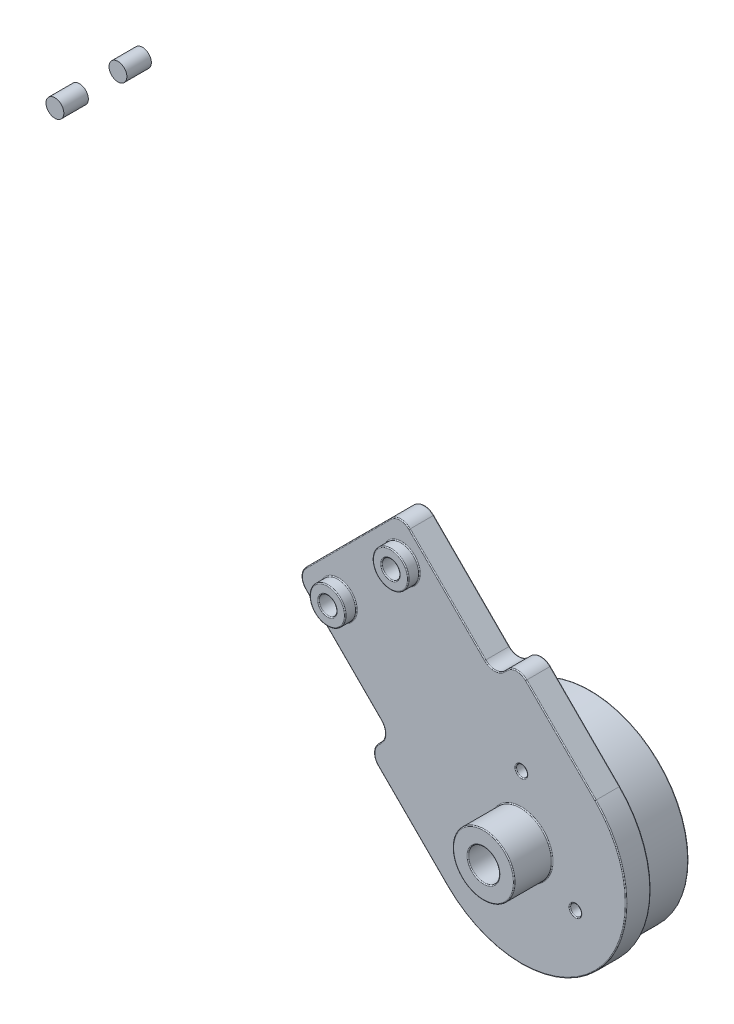
SolidWorks part; units mm, degrees
ref_plane "Front Plane" through (0, 0, 0) normal (0, 0, 1) x (1, 0, 0)
ref_plane "Top Plane" through (0, 0, 0) normal (0, 1, 0) x (1, 0, 0)
ref_plane "Right Plane" through (0, 0, 0) normal (1, 0, 0) x (0, 0, -1)
sketch "Sketch1" plane through (0, 0, 0) normal (0, 0, 1) x (1, 0, 0)
  line L0 (-100, 0) -> (100, 0) construction
  line L1 (-100, 0) -> (0, 100) construction
  line L2 (0, 100) -> (100, 0) construction
  line L3 (0, 0) -> (-50, 50) construction
  line L4 (-40, 60) -> (40, 60) construction
  line L5 (0, 100) -> (0, 60) construction
  line L6 (-56.5165, 43.4835) -> (-40, 60)
  line L7 (-40, 60) -> (40, 60)
  line L8 (40, 60) -> (86.565, 13.435) construction
  line L9 (-49.4454, 36.4124) -> (-35.8579, 50)
  line L10 (-35.8579, 50) -> (35.8579, 50)
  line L11 (35.8579, 50) -> (79.4939, 6.364)
  line L12 (-63.5876, 50.5546) -> (-44.1421, 70)
  line L13 (-44.1421, 70) -> (44.1421, 70)
  line L14 (44.1421, 70) -> (93.636, 20.5061)
  line L15 (-63.5876, 50.5546) -> (-49.4454, 36.4124)
  line L16 (93.636, 20.5061) -> (79.4939, 6.364)
  line L17 (91.1612, 18.0312) -> (104.5962, 4.5962)
  line L18 (81.9688, 8.8388) -> (95.4038, -4.5962)
  line L19 (58.2807, 55.8614) -> (44.1386, 41.7193) construction
  line L20 (6, 70) -> (3.4304, 82.6944)
  line L21 (-6, 70) -> (-3.4304, 82.6944)
  line L22 (40, 60) -> (86.565, 13.435)
  circle A0 centre (-100, 0) radius 20
  circle A1 centre (0, 0) radius 20
  circle A2 centre (100, 0) radius 20
  circle A3 centre (100, 0) radius 10 construction
  circle A4 centre (100, 0) radius 3.5
  arc A5 (95.4038, -4.5962) -> (104.5962, 4.5962) centre (100, 0) ccw
  circle A6 centre (100, 0) radius 6.5 construction
  circle A7 centre (47.6741, 45.2548) radius 1
  circle A8 centre (54.7452, 52.3259) radius 1
  circle A9 centre (0, 60) radius 1.5
  circle A10 centre (0, 82) radius 1.5
  arc A11 (3.4304, 82.6944) -> (-3.4304, 82.6944) centre (0, 82) ccw
  circle A12 centre (0, 82) radius 3.5 construction
  circle A13 centre (-50, 50) radius 1.5
  point P2 (0, 0)
  dimension "D5" = 40
  dimension "D9" = 20
  dimension "D10" = 7
  dimension "D14" = 2
  dimension "D17" = 3
  dimension "D22" = 3
  dimension "D1" = 200
  dimension "D2" = 90
  dimension "D3" = 90
  dimension "D4" = 80
  dimension "D8" = 27.5
  dimension "D12" = 19
  dimension "D13" = 50
  dimension "D15" = 5
  dimension "D16" = 5
  dimension "D18" = 12
  dimension "D20" = 6
  dimension "D21" = 6
  dimension "D6" = 10
  dimension "D7" = 10
  dimension "D11" = 3
  dimension "D19" = 2
sketch "Sketch2" plane through (0, 0, 0) normal (0, 0, 1) x (1, 0, 0)
  line L0 (-86.565, 13.435) -> (-50, 50) construction
  line L1 (-100, 0) -> (0, 100) construction
  line L2 (-50, 50) -> (-13.435, 13.435) construction
  line L3 (0, 0) -> (-50, 50) construction
  line L4 (-79.4939, 6.364) -> (-50, 35.8579)
  line L5 (-50, 35.8579) -> (-20.5061, 6.364)
  line L6 (-93.636, 20.5061) -> (-50, 64.1421)
  line L7 (-50, 64.1421) -> (-6.364, 20.5061)
  line L8 (-93.636, 20.5061) -> (-50, 64.1421) construction
  line L9 (-79.4939, 6.364) -> (-50, 35.8579) construction
  line L10 (-93.636, 20.5061) -> (-79.4939, 6.364)
  line L11 (-6.364, 20.5061) -> (-20.5061, 6.364)
  line L12 (-104.534, 4.6576) -> (-90.9809, 17.8509)
  line L13 (-95.3424, -4.534) -> (-82.1491, 9.0191)
  line L14 (-18.0312, 8.8388) -> (-4.5962, -4.5962)
  line L15 (-8.8388, 18.0312) -> (4.5962, 4.5962)
  line L16 (-91.8683, 22.2739) -> (-77.7261, 8.1317) construction
  line L17 (-8.1317, 22.2739) -> (-22.2739, 8.1317) construction
  circle A0 centre (-100, 0) radius 3.5
  circle A1 centre (-100, 0) radius 10 construction
  circle A2 centre (0, 0) radius 3.5
  circle A3 centre (0, 0) radius 10 construction
  arc A4 (-4.5962, -4.5962) -> (4.5962, 4.5962) centre (0, 0) ccw
  arc A5 (-104.534, 4.6576) -> (-95.3424, -4.534) centre (-100, 0) ccw
  circle A6 centre (-100, 0) radius 20 construction
  circle A7 centre (-100, 0) radius 6.5 construction
  circle A8 centre (0, 0) radius 6.5 construction
  circle A9 centre (-88.3327, 18.7383) radius 1
  circle A10 centre (-81.2617, 11.6673) radius 1
  circle A11 centre (-18.7383, 11.6673) radius 1
  circle A12 centre (-11.6673, 18.7383) radius 1
  dimension "D1" = 20
  dimension "D2" = 7
  dimension "D8" = 2
  dimension "D6" = 19
  dimension "D7" = 19
  dimension "D9" = 5
  dimension "D10" = 5
  dimension "D11" = 5
  dimension "D12" = 5
  dimension "D13" = 5
  dimension "D14" = 5
  dimension "D3" = 3
  dimension "D4" = 10
  dimension "D5" = 10
sketch "Sketch3" plane through (0, 0, 0) normal (0, 0, 1) x (1, 0, 0)
  line L0 (86.3882, 25.2791) -> (74.7209, 13.6118)
  line L1 (40, 60) -> (86.565, 13.435) construction
  line L2 (74.7209, 13.6118) -> (85.3275, 3.0052)
  line L3 (85.3275, 3.0052) -> (82.8527, 0.5303)
  line L4 (82.8527, 0.5303) -> (91.6915, -8.3085)
  line L5 (100, 0) -> (88.4062, 11.5938) construction
  line L6 (0, 100) -> (100, 0) construction
  line L7 (99.4697, 17.1473) -> (108.3085, 8.3085)
  line L8 (96.9948, 14.6725) -> (99.4697, 17.1473)
  line L9 (86.3882, 25.2791) -> (96.9948, 14.6725)
  circle A0 centre (100, 0) radius 10 construction
  circle A1 centre (100, 0) radius 10
  arc A2 (91.6915, -8.3085) -> (108.3085, 8.3085) centre (100, 0) ccw
  circle A3 centre (100, 0) radius 11.75 construction
  circle A4 centre (47.6741, 45.2548) radius 1 construction
  circle A5 centre (54.7452, 52.3259) radius 1 construction
  circle A6 centre (47.6741, 45.2548) radius 1
  circle A7 centre (54.7452, 52.3259) radius 1
  point P7 (80.5546, 19.4454)
  dimension "D2" = 16.5
  dimension "D3" = 12.5
  dimension "D4" = 15
  dimension "D1" = 1.75
extrude "Boss-Extrude1" add sketch "Sketch3" along normal blind 2.75
sketch "Sketch4" plane through (0, 0, 2.75) normal (0, 0, 1) x (1, 0, 0)
  circle A0 centre (100, 0) radius 10 construction
  circle A1 centre (100, 0) radius 10
extrude "Boss-Extrude3" add sketch "Sketch4" against normal blind 1
sketch "Sketch5" plane through (0, 0, 0) normal (0, 0, -1) x (-1, 0, 0)
  circle A0 centre (-100, 0) radius 11
  circle A1 centre (-100, 0) radius 10
  circle A2 centre (-100, 0) radius 10
  dimension "D1" = 0
  dimension "D2" = 1
extrude "Boss-Extrude4" add sketch "Sketch5" along normal blind 5
fillet "Fillet1" radius 1.5 6 edges at (96.9948, 14.6725, 1.375) (99.4697, 17.1473, 1.375) (82.8527, 0.5303, 1.375) (85.3275, 3.0052, 1.375) (74.7209, 13.6118, 1.375) (86.3882, 25.2791, 1.375)
sketch "Sketch6" plane through (0, 0, 2.75) normal (0, 0, 1) x (1, 0, 0)
  circle A0 centre (79.4939, 13.435) radius 1 construction
  circle A1 centre (86.565, 20.5061) radius 1 construction
  circle A2 centre (79.4939, 13.435) radius 1
  circle A3 centre (86.565, 20.5061) radius 1
  circle A4 centre (86.565, 20.5061) radius 2
  circle A5 centre (79.4939, 13.435) radius 2
  dimension "D1" = 1
extrude "Boss-Extrude5" add sketch "Sketch6" along normal blind 1.25
sketch "Sketch7" plane through (0, 0, 2.75) normal (0, 0, 1) x (1, 0, 0)
  circle A0 centre (100, 0) radius 1.75
  dimension "D1" = 3.5
extrude "Cut-Extrude1" cut sketch "Sketch7" against normal up to surface (1 mm away) up to face at (110, 0, 1.75)
sketch "Sketch8" plane through (0, 0, 2.75) normal (0, 0, 1) x (1, 0, 0)
  circle A0 centre (100, 0) radius 1.75 construction
  circle A1 centre (100, 0) radius 1.75
  circle A2 centre (100, 0) radius 3.45
  dimension "D1" = 6.9
extrude "Boss-Extrude6" add sketch "Sketch8" along normal blind 4.25
sketch "Sketch9" plane through (0, 0, 2.75) normal (0, 0, 1) x (1, 0, 0)
  line L0 (100, 0) -> (100, 7) construction
  circle A0 centre (100, 7) radius 0.625
  circle A1 centre (106.0622, -3.5) radius 0.625
  circle A2 centre (93.9378, -3.5) radius 0.625
  dimension "D1" = 1.25
  dimension "D2" = 7
  dimension "D3" = 3
extrude "Cut-Extrude2" cut sketch "Sketch9" against normal up to surface (1 mm away) up to face at (101.75, 0, 1.75)
fillet "Fillet2" radius 0.1 48 edges at (94.5628, -3.5, 2.75) (94.5628, -3.5, 1.75) (106.6872, -3.5, 2.75) (106.6872, -3.5, 1.75) (100.625, 7, 2.75) (100.625, 7, 1.75) (101.75, 0, 7) (103.45, 0, 2.75) (103.45, 0, 7) (101.75, 0, 1.75) (80.4939, 13.435, 4) (81.4939, 13.435, 2.75) (81.4939, 13.435, 4) (87.565, 20.5061, 4) (88.565, 20.5061, 2.75) (88.565, 20.5061, 4) (90, 0, -5) (89, 0, -5) (110, 0, 1.75) (91.6915, 19.9758, 0) (80.5546, 19.4454, 0) (80.0242, 8.3085, 0) (84.0901, 1.7678, 0) (87.8024, -4.4194, 0) (108.3085, -8.3085, 0) (104.4194, 12.1976, 0) (98.2322, 15.9099, 0) (91.6915, 19.9758, 2.75) (80.5546, 19.4454, 2.75) (80.0242, 8.3085, 2.75) (84.0901, 1.7678, 2.75) (87.8024, -4.4194, 2.75) (108.3085, -8.3085, 2.75) (98.2322, 15.9099, 2.75) (111, 0, 0) (86.3882, 24.6577, 0) (75.3423, 13.6118, 0) (83.474, 0.5303, 0) (99.4697, 16.526, 0) (86.3882, 24.6577, 2.75) (75.3423, 13.6118, 2.75) (83.474, 0.5303, 2.75) (99.4697, 16.526, 2.75) (96.9948, 15.2938, 0) (96.9948, 15.2938, 2.75) (84.7062, 3.0052, 0) (84.7062, 3.0052, 2.75) (104.4194, 12.1976, 2.75)
sketch "Sketch12" plane through (0, 0, 0) normal (0, 0, 1) x (1, 0, 0)
  circle A0 centre (86.565, 20.5061) radius 1
  circle A1 centre (79.4939, 13.435) radius 1
extrude "Cut-Extrude4" cut sketch "Sketch12" against normal through all both and the other way through all
